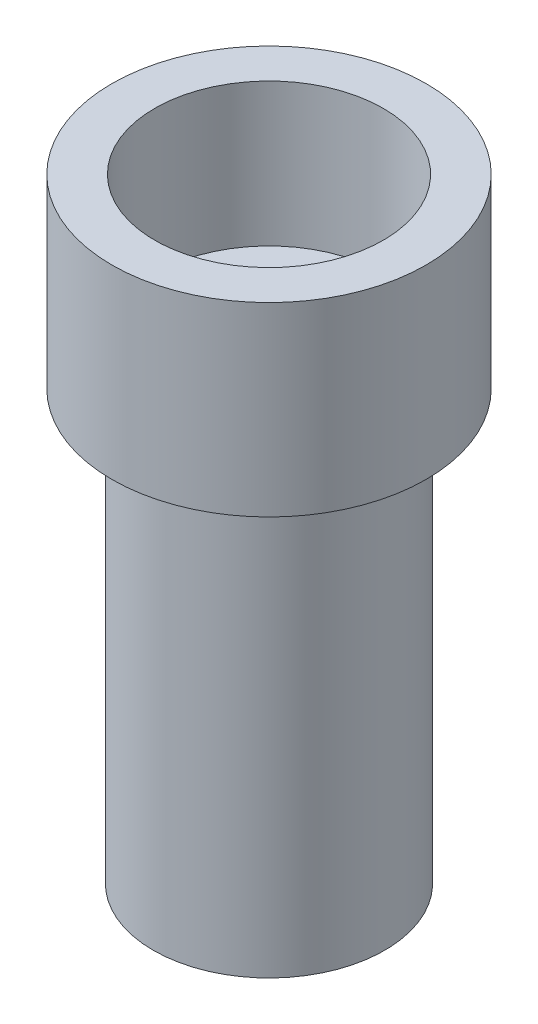
SolidWorks part; units mm, degrees
ref_plane "Plano frontal" through (0, 0, 0) normal (0, 0, 1) x (1, 0, 0)
ref_plane "Plano superior" through (0, 0, 0) normal (0, 1, 0) x (1, 0, 0)
ref_plane "Plano direito" through (0, 0, 0) normal (1, 0, 0) x (0, 0, -1)
sketch "Esboço1" plane through (0, 0, 0) normal (0, 0, 1) x (1, 0, 0)
  line L0 (4, 21.5) -> (5.5, 21.5)
  line L1 (5.5, 21.5) -> (5.5, 15)
  line L2 (5.5, 15) -> (4.05, 15)
  line L3 (4.05, 15) -> (4.05, 0)
  line L4 (4.05, 0) -> (0, 0)
  line L5 (0, 0) -> (0, 16.5)
  line L6 (0, 16.5) -> (4, 16.5)
  line L7 (4, 16.5) -> (4, 21.5)
  line L8 (0, 0) -> (0, 18.2739) construction
  point P11 (0, 10.5017)
  point P12 (3.9, 18.2739)
  dimension "D1" = 8.1
  dimension "D2" = 8
  dimension "D3" = 1.5
  dimension "D4" = 15
  dimension "D5" = 5
  dimension "D6" = 1.5
revolve "Revolução1" add sketch "Esboço1" angle 360 about L8
